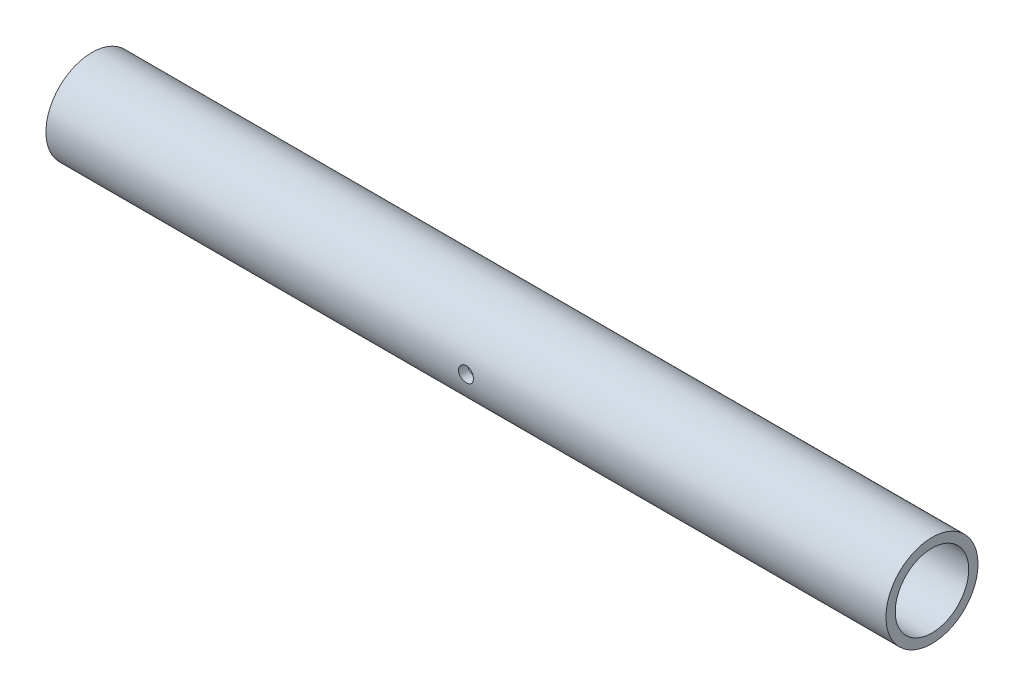
SolidWorks part; units mm, degrees
ref_plane "Front Plane" through (0, 0, 0) normal (0, 0, 1) x (1, 0, 0)
ref_plane "Top Plane" through (0, 0, 0) normal (0, 1, 0) x (1, 0, 0)
ref_plane "Right Plane" through (0, 0, 0) normal (1, 0, 0) x (0, 0, -1)
sketch "Sketch1" plane through (0, 0, 0) normal (1, 0, 0) x (0, 0, -1)
  circle A0 centre (0, 0) radius 16.7005
  circle A1 centre (0, 0) radius 13.335
  dimension "D1" = 33.401
  dimension "D2" = 26.67
extrude "Boss-Extrude1" add sketch "Sketch1" along normal blind 304.8
hole_wizard "1/4-28 Tapped Hole1" positions "3DSketch2" profile "Sketch3" tap size "1/4-28" standard "ANSI Inch"
sketch3d "3DSketch2"
  point P0 (152.4, 0, 16.7005)
sketch "Sketch3" plane through (152.4, 0, 16.7005) normal (1, 0, 0) x (0, -1, 0)
  line L0 (0, 0) -> (0, 3.3655)
  line L1 (0, 3.3655) -> (2.7051, 3.3655)
  line L2 (2.7051, 3.3655) -> (2.7051, 0)
  line L5 (2.7051, 0) -> (0, 0)
  line L11 (0, -6.35) -> (0, 107.95) construction
  dimension "Thru Tap Drill Dia." = 5.4102
  dimension "Thru Tap Drill Depth" = 3.3655
cosmetic thread "Hole Thread1"
